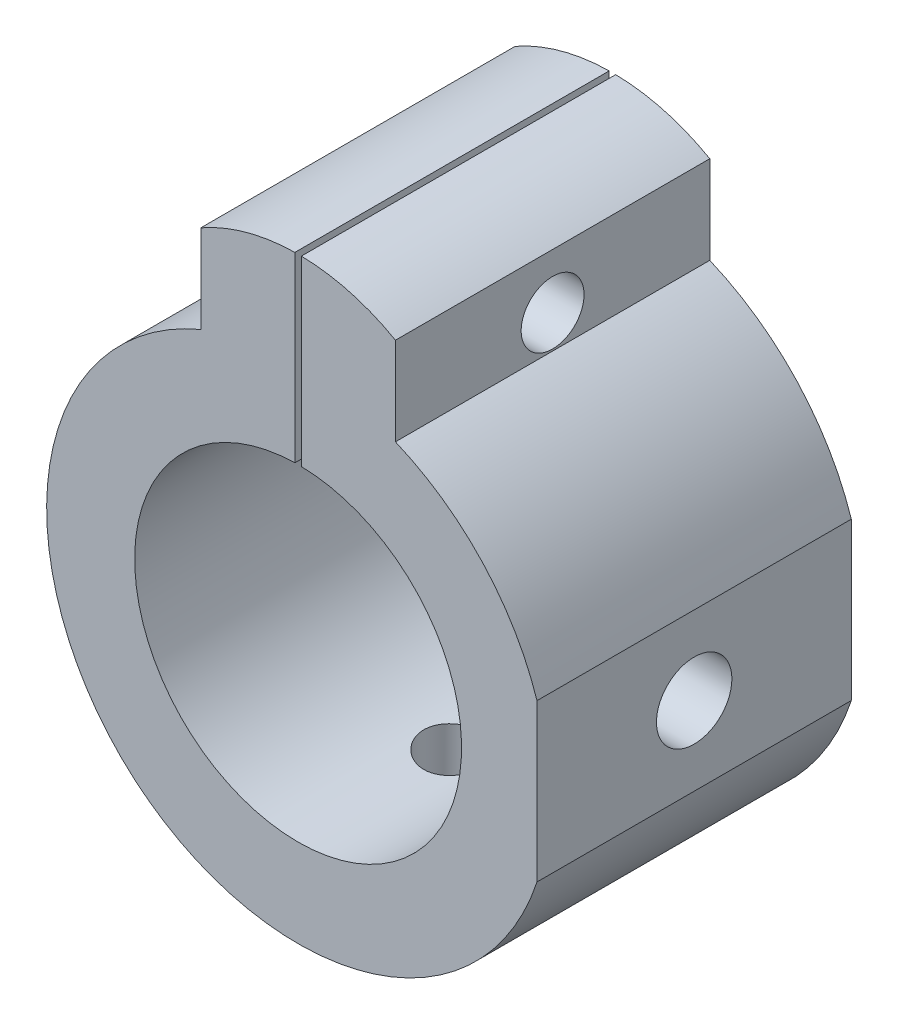
SolidWorks part; units mm, degrees
material "6061 合金"
ref_plane "前视基准面" through (0, 0, 0) normal (0, 0, 1) x (1, 0, 0)
ref_plane "上视基准面" through (0, 0, 0) normal (0, 1, 0) x (1, 0, 0)
ref_plane "右视基准面" through (0, 0, 0) normal (1, 0, 0) x (0, 0, -1)
sketch "草图1" plane through (0, 0, 0) normal (0, 0, 1) x (1, 0, 0)
  line L0 (-7.7403, 18.4415) -> (-7.7403, 25.4415)
  line L1 (-35, -7) -> (-35, 7)
  line L2 (-35, 7) -> (-7.7403, 18.4415)
  line L3 (-35, -7) -> (-7.7403, -18.4415)
  line L4 (7.7403, 18.4415) -> (7.7403, 25.4415)
  line L5 (35, -7) -> (7.7403, -18.4415)
  line L6 (35, -7) -> (35, 7)
  line L7 (35, 7) -> (7.7403, 18.4415)
  line L8 (0, 0) -> (-28, 0) construction
  circle A0 centre (0, 0) radius 13
  arc A1 (-7.7403, 18.4415) -> (7.7403, 18.4415) centre (0, 0) ccw
  arc A2 (-7.7403, 25.4415) -> (7.7403, 25.4415) centre (0, 11.8749) cw
  circle A3 centre (-28, 0) radius 3.5
  circle A4 centre (28, 0) radius 3.5
  dimension "D1" = 28
  dimension "D3" = 26
  dimension "D4" = 20
  dimension "D5" = 7
  dimension "D6" = 7
  dimension "D2" = 28
  dimension "D7" = 70
extrude "凸台-拉伸2" add sketch "草图1" along normal blind 10 contours A1 L5 L6 L7 | A2 L0 A1 L4 A0 | A1 L2 L1 L3
sketch "草图2" plane through (0, 0, 10) normal (0, 0, 1) x (1, 0, 0)
  line L0 (-7.7403, 18.4415) -> (-7.7403, 25.4415)
  line L1 (7.7403, 18.4415) -> (7.7403, 25.4415)
  circle A0 centre (0, 0) radius 13
  arc A1 (-7.7403, 18.4415) -> (7.7403, 18.4415) centre (0, 0) ccw
  arc A2 (-7.7403, 25.4415) -> (7.7403, 25.4415) centre (0, 11.8749) cw
extrude "凸台-拉伸3" add sketch "草图2" along normal blind 15
sketch "草图3" plane through (0, 0, 25) normal (0, 0, 1) x (1, 0, 0)
  line L1 (-0.2586, 12.3781) -> (-0.2586, 31.1043)
  line L2 (0.2586, 12.3781) -> (0.2586, 31.1043)
  line L3 (-0.2586, 12.3781) -> (0.2586, 12.3781)
  line L4 (-0.2586, 31.1043) -> (0.2586, 31.1043)
extrude "切除-拉伸1" cut sketch "草图3" against normal through all
sketch "草图4" plane through (7.7403, 0, 0) normal (1, 0, 0) x (0, 0, -1)
  circle A0 centre (-12.5, 21.0864) radius 2.5
extrude "切除-拉伸2" cut sketch "草图4" against normal through all
sketch "草图5" plane through (0, 0, 10) normal (0, 0, 1) x (1, 0, 0)
  line L0 (-7.7403, 18.4415) -> (-35, 7)
  line L1 (-35, 7) -> (-35, -7)
  line L2 (-35, -7) -> (-7.7403, -18.4415)
  line L3 (7.7403, 18.4415) -> (35, 7)
  line L4 (35, 7) -> (35, -7)
  line L5 (35, -7) -> (7.7403, -18.4415)
  arc A0 (-7.7403, 18.4415) -> (-7.7403, -18.4415) centre (0, 0) ccw
  arc A1 (7.7403, -18.4415) -> (7.7403, 18.4415) centre (0, 0) ccw
extrude "切除-拉伸3" cut sketch "草图5" against normal through all
sketch "草图6" plane through (0, 0, 0) normal (0, 1, 0) x (1, 0, 0)
  line L0 (0, 0) -> (0, -25) construction
  line L1 (-20, -25) -> (20, -25) construction
  circle A0 centre (0, -12.5) radius 2.5
  dimension "D1" = 5
extrude "切除-拉伸4" cut sketch "草图6" against normal through all contours A0
sketch "草图8" plane through (0, 0, 0) normal (0, 0, 1) x (1, 0, 0)
  line L0 (0, 0) -> (30.3536, 0) construction
  line L1 (24, 15) -> (19, 15)
  line L2 (24, 15) -> (24, -15)
  line L3 (24, -15) -> (19, -15)
  line L4 (19, 15) -> (19, -15)
  dimension "D1" = 30
  dimension "D2" = 5
  dimension "D3" = 19
extrude "切除-拉伸5" cut sketch "草图8" along normal through all
sketch "草图9" plane through (19, 0, 0) normal (1, 0, 0) x (0, 0, -1)
  line L0 (0, 0) -> (-25, 0) construction
  line L1 (-25, -6.245) -> (-25, 6.245) construction
  circle A0 centre (-12.5, 0) radius 3
  dimension "D1" = 6
extrude "切除-拉伸6" cut sketch "草图9" against normal blind 10
cosmetic thread "装饰螺纹线1" parameters "D2"=8
